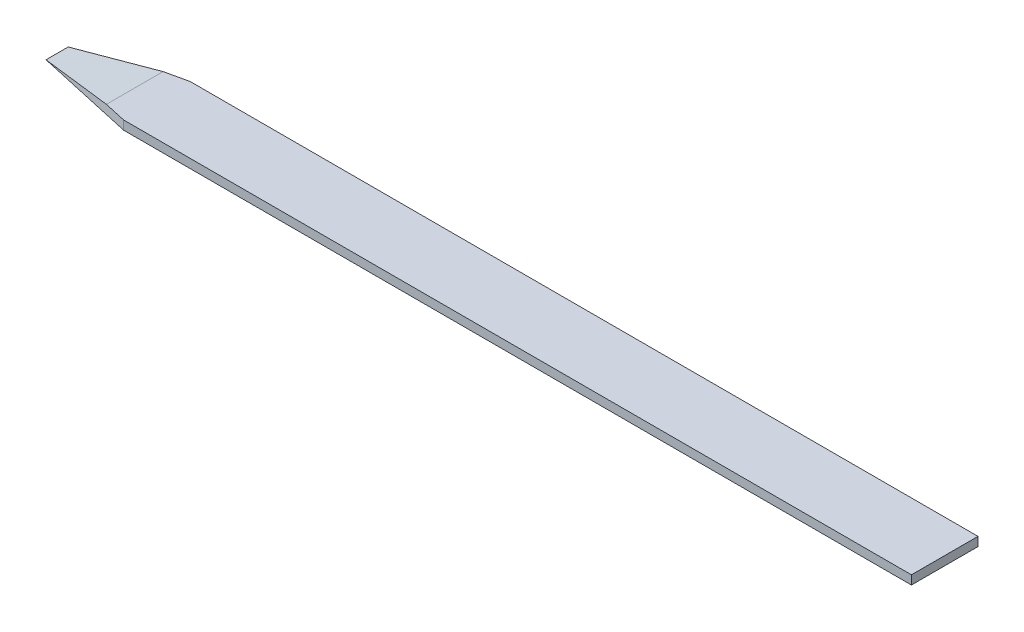
SolidWorks part; units mm, degrees
ref_plane "Front Plane" through (0, 0, 0) normal (0, 0, 1) x (1, 0, 0)
ref_plane "Top Plane" through (0, 0, 0) normal (0, 1, 0) x (1, 0, 0)
ref_plane "Right Plane" through (0, 0, 0) normal (1, 0, 0) x (0, 0, -1)
sketch "Sketch1" plane through (0, 0, 0) normal (0, 1, 0) x (1, 0, 0)
  line L0 (0, 0.35) -> (0, -0.25)
  line L1 (-8, -0.25) -> (0, -0.25)
  line L2 (-8, -0.25) -> (-8, 0.35)
  line L3 (0, -0.25) -> (0, 0.35)
  line L4 (-8, 0.35) -> (0, 0.35)
  line L5 (-8, -0.25) -> (0, 0.35) construction
  line L6 (0, -0.25) -> (-8, 0.35) construction
  line L7 (0, 0.35) -> (0, -0.25)
  line L9 (-4, -0.25) -> (-8, -0.25)
  line L10 (-8, 0.35) -> (-4, 0.35)
  point P6 (-4, 0.05)
  dimension "D3" = 8
  dimension "D4" = 0.6
extrude "Boss-Extrude1" add sketch "Sketch1" along normal blind 0.08
sketch "Sketch5" plane through (0, 0, 0.25) normal (0, 0, 1) x (1, 0, 0)
  line L0 (-8, 0) -> (-8, 0.08)
  line L1 (-8, 0.08) -> (-7.3, 0.08)
  line L3 (-7.3, 0.08) -> (-8, 0)
  line L4 (-8, 0.08) -> (0, 0.08) construction
  line L5 (-8, 0) -> (0, 0) construction
  dimension "D1" = 0.7
extrude "Cut-Extrude3" cut sketch "Sketch5" against normal through all contours L3 L0 L1
sketch3d "3DSketch1"
  line L0 (-7.3, 0.08, -0.35) -> (-7.3, 0.08, 0.25)
  line L10 (0, 0.08, -0.35) -> (0, 0.08, 0.25) construction
  line L11 (-7.1, 0.08, 0.25) -> (-8, 0.08, 0.25)
  line L12 (-7.3, 0.08, -0.35) -> (0, 0.08, -0.35) construction
  line L13 (0, 0.08, -0.05) -> (-7.2904, 0.08, -0.05) construction
  line L14 (-7.3, 0.08, 0.25) -> (0, 0.08, 0.25) construction
  line L15 (-8, 0.08, 0.25) -> (-8, 0.08, 0.05)
  line L16 (-8, 0.08, 0.05) -> (-7.1, 0.08, 0.25)
  line L18 (-7.1, 0.08, -0.35) -> (-8, 0.08, -0.35)
  line L19 (-8, 0.08, -0.35) -> (-8, 0.08, -0.15)
  line L20 (-8, 0.08, -0.15) -> (-7.1, 0.08, -0.35)
  line L21 (-7.3, 0.08, -0.35) -> (-7.3, 0.08, 0.25) construction
  line L22 (-8, 0.08, -0.15) -> (-8, 0.08, 0.05) construction
  point P18 (-8, 0.08, -0.05)
  dimension "D1" = 0.7
  dimension "D2" = 0.9
  dimension "D3" = 0.7
  dimension "D4" = 0.9
  dimension "D5" = 0.2
extrude "Cut-Extrude4" cut sketch "3DSketch1" along direction (0, -1, 0) on the side against the normal through all
